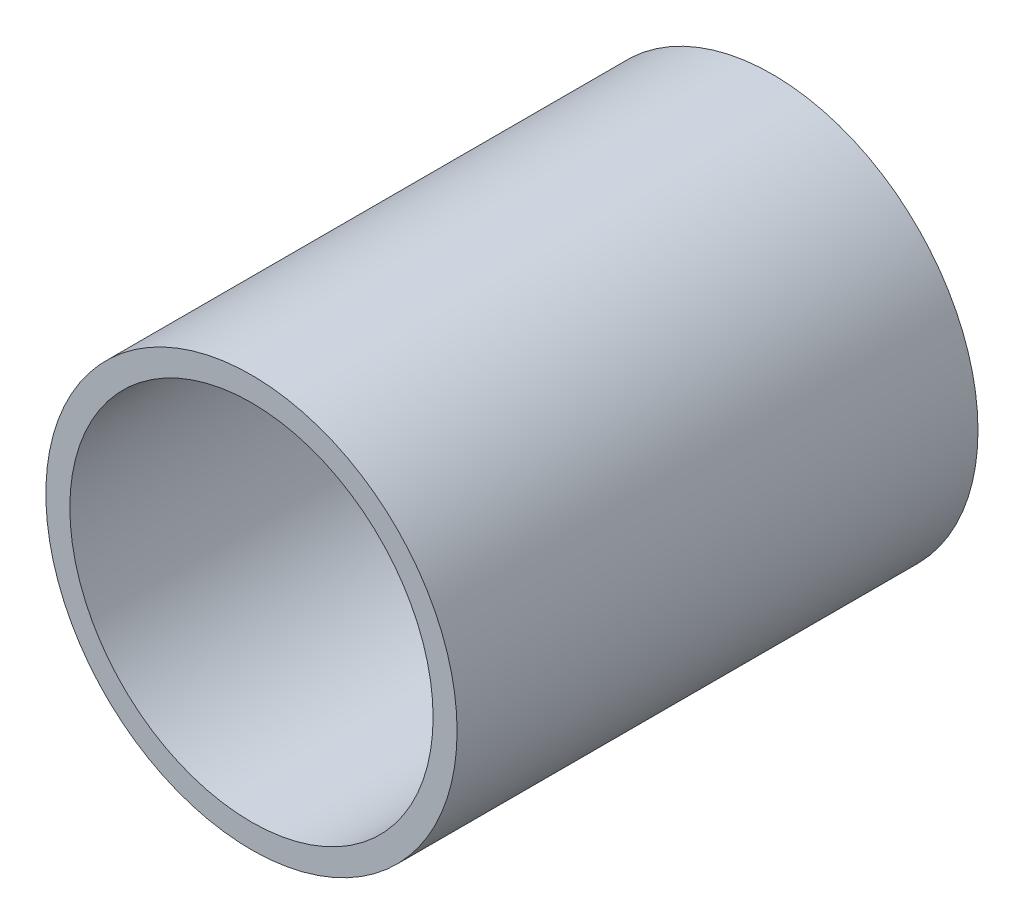
SolidWorks part; units mm, degrees
ref_plane "Front Plane" through (0, 0, 0) normal (0, 0, 1) x (1, 0, 0)
ref_plane "Top Plane" through (0, 0, 0) normal (0, 1, 0) x (1, 0, 0)
ref_plane "Right Plane" through (0, 0, 0) normal (1, 0, 0) x (0, 0, -1)
sketch "Sketch1" plane through (0, 0, 0) normal (0, 0, 1) x (1, 0, 0)
  circle A0 centre (0, 0) radius 19.05
  circle A1 centre (0, 0) radius 16.8275
  dimension "D1" = 38.1
  dimension "D2" = 33.655
extrude "Boss-Extrude1" add sketch "Sketch1" along normal blind 48.26
